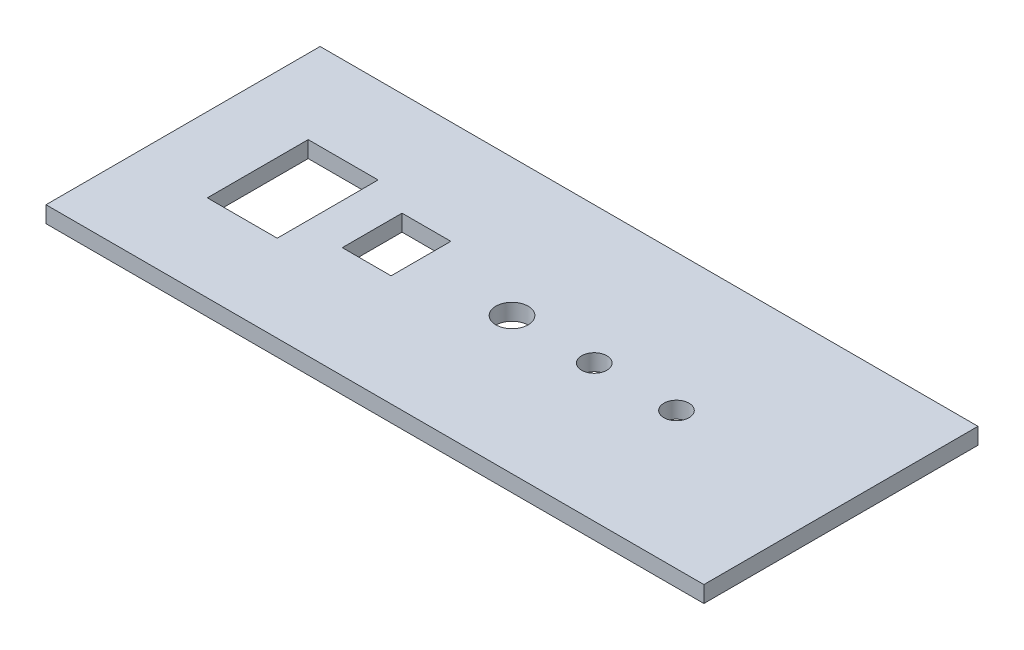
SolidWorks part; units mm, degrees
ref_plane "Front Plane" through (0, 0, 0) normal (0, 0, 1) x (1, 0, 0)
ref_plane "Top Plane" through (0, 0, 0) normal (0, 1, 0) x (1, 0, 0)
ref_plane "Right Plane" through (0, 0, 0) normal (1, 0, 0) x (0, 0, -1)
sketch "Sketch1" plane through (0, 0, 0) normal (0, 1, 0) x (1, 0, 0)
  line L1 (0, 0) -> (-120, 0)
  line L2 (0, 0) -> (0, 50)
  line L3 (0, 50) -> (-120, 50)
  line L4 (-120, 0) -> (-120, 50)
  dimension "D1" = 120
  dimension "D2" = 50
extrude "Boss-Extrude1" add sketch "Sketch1" along normal blind 3
sketch "Sketch2" plane through (0, 3, 0) normal (0, 1, 0) x (1, 0, 0)
  line L0 (-120, 25) -> (0, 25) construction
  line L1 (-120, 50) -> (-120, 0) construction
  line L2 (0, 0) -> (0, 50) construction
  line L4 (-93.625, 15.8) -> (-106.375, 15.8)
  line L5 (-93.625, 15.8) -> (-93.625, 34.2)
  line L6 (-93.625, 34.2) -> (-106.375, 34.2)
  line L7 (-106.375, 15.8) -> (-106.375, 34.2)
  line L8 (-93.625, 15.8) -> (-106.375, 34.2) construction
  line L9 (-93.625, 34.2) -> (-106.375, 15.8) construction
  circle A0 centre (-60, 25) radius 2.95
  circle A1 centre (-45, 25) radius 2.3
  circle A2 centre (-30, 25) radius 2.3
  point P12 (-100, 25)
  dimension "D1" = 5.9
  dimension "D2" = 4.6
  dimension "D3" = 4.6
  dimension "D8" = 18.4
  dimension "D4" = 20
  dimension "D5" = 60
  dimension "D6" = 75
  dimension "D7" = 90
  dimension "D9" = 12.75
extrude "Cut-Extrude1" cut sketch "Sketch2" against normal blind 3
sketch "Sketch3" plane through (0, 3, 0) normal (0, 1, 0) x (1, 0, 0)
  line L1 (-77.2974, 20.2403) -> (-86.1974, 20.2403)
  line L2 (-77.2974, 20.2403) -> (-77.2974, 31.1403)
  line L3 (-77.2974, 31.1403) -> (-86.1974, 31.1403)
  line L4 (-86.1974, 20.2403) -> (-86.1974, 31.1403)
  line L5 (-77.2974, 20.2403) -> (-86.1974, 31.1403) construction
  line L6 (-77.2974, 31.1403) -> (-86.1974, 20.2403) construction
  point P0 (-81.7474, 25.6903)
  dimension "D1" = 10.9
  dimension "D2" = 8.9
extrude "Cut-Extrude2" cut sketch "Sketch3" against normal blind 10
